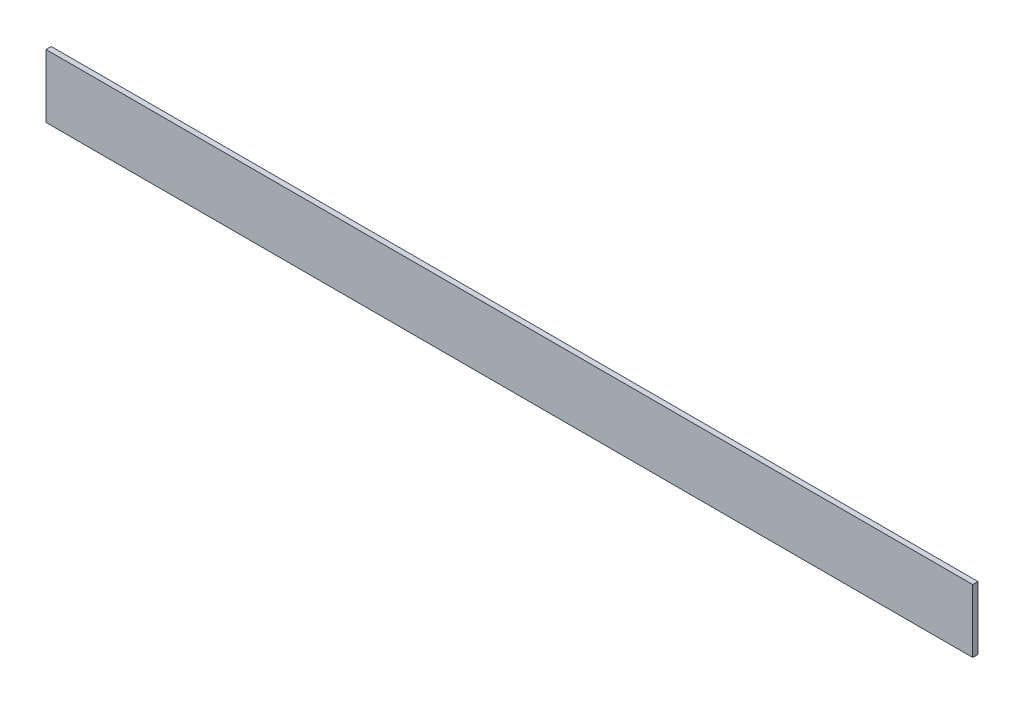
SolidWorks part; units mm, degrees
material "PVC 0.007 Plasticized"
ref_plane "Front Plane" through (0, 0, 0) normal (0, 0, 1) x (1, 0, 0)
ref_plane "Top Plane" through (0, 0, 0) normal (0, 1, 0) x (1, 0, 0)
ref_plane "Right Plane" through (0, 0, 0) normal (1, 0, 0) x (0, 0, -1)
sketch "Sketch1" plane through (0, 0, 0) normal (1, 0, 0) x (0, 0, -1)
  line L1 (-3.175, -38.1) -> (3.175, -38.1)
  line L2 (-3.175, -38.1) -> (-3.175, 38.1)
  line L3 (-3.175, 38.1) -> (3.175, 38.1)
  line L4 (3.175, -38.1) -> (3.175, 38.1)
  line L5 (-3.175, -38.1) -> (3.175, 38.1) construction
  line L6 (-3.175, 38.1) -> (3.175, -38.1) construction
  point P0 (0, 0)
  dimension "D1" = 76.2
  dimension "D2" = 6.35
extrude "Boss-Extrude1" add sketch "Sketch1" along normal blind 1117.6
equation "\"D2@Sketch1\"=1in/4"
equation "\"D1@Boss-Extrude1\"=44in"
